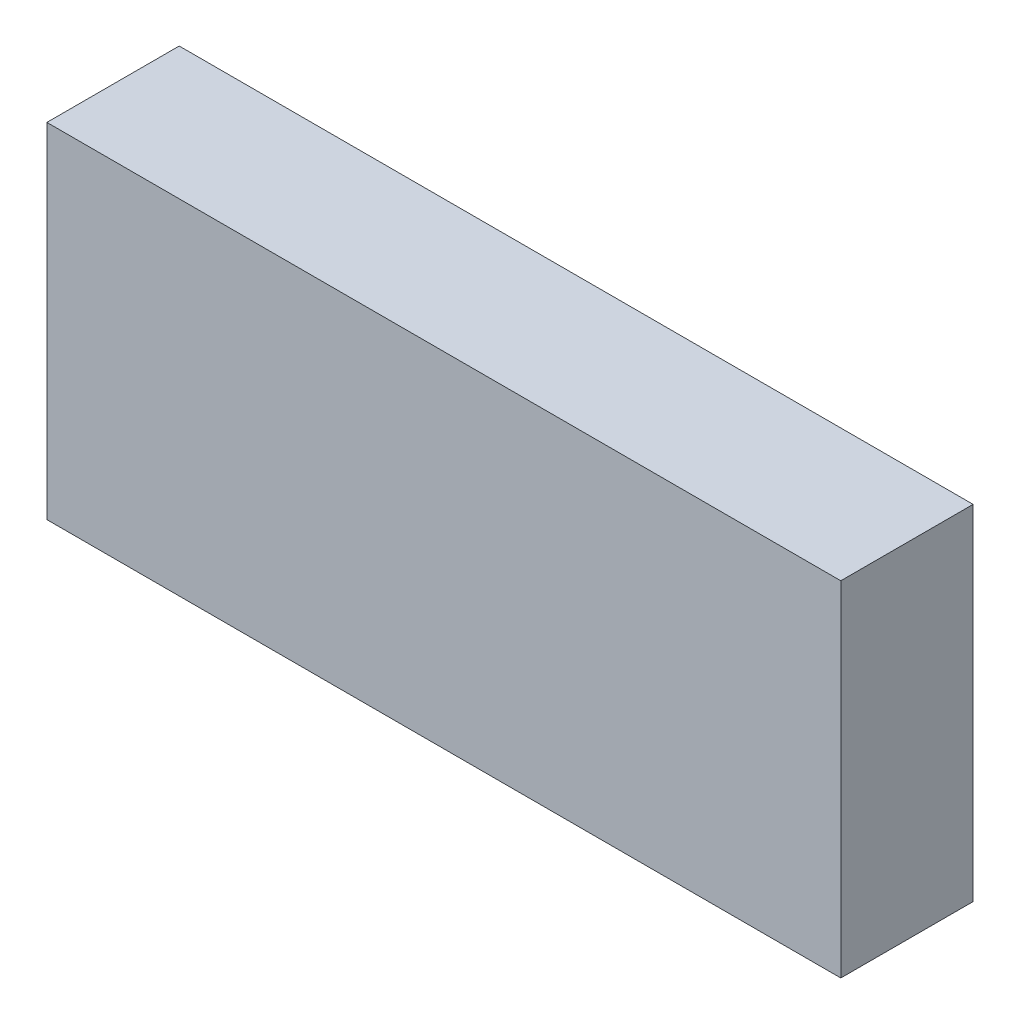
SolidWorks part; units mm, degrees
ref_plane "Front Plane" through (0, 0, 0) normal (0, 0, 1) x (1, 0, 0)
ref_plane "Top Plane" through (0, 0, 0) normal (0, 1, 0) x (1, 0, 0)
ref_plane "Right Plane" through (0, 0, 0) normal (1, 0, 0) x (0, 0, -1)
sketch "Sketch1" plane through (0, 0, 0) normal (0, 0, 1) x (1, 0, 0)
  line L1 (-19.05, -8.255) -> (19.05, -8.255)
  line L2 (-19.05, -8.255) -> (-19.05, 8.255)
  line L3 (-19.05, 8.255) -> (19.05, 8.255)
  line L4 (19.05, -8.255) -> (19.05, 8.255)
  line L5 (-19.05, -8.255) -> (19.05, 8.255) construction
  line L6 (-19.05, 8.255) -> (19.05, -8.255) construction
  point P0 (0, 0)
  dimension "D1" = 16.51
  dimension "D2" = 38.1
extrude "Boss-Extrude1" add sketch "Sketch1" along normal mid plane 6.35
